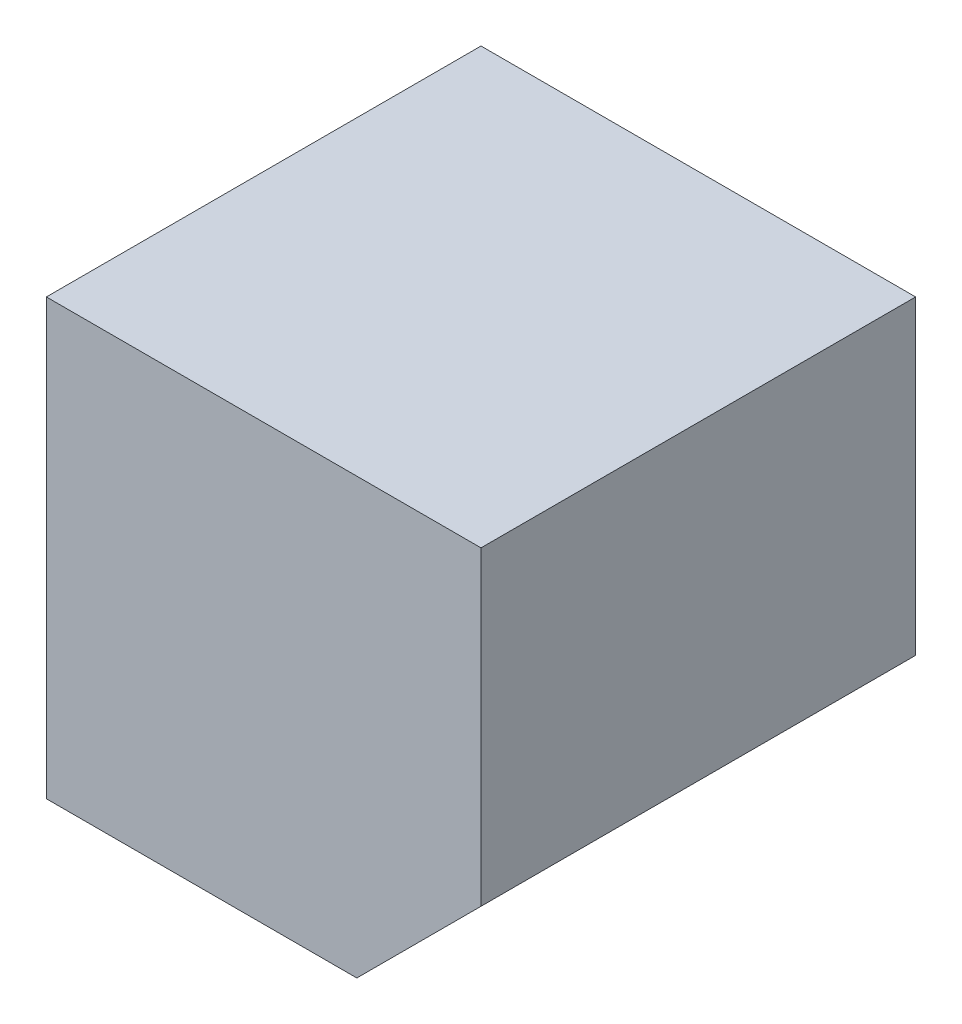
SolidWorks part; units mm, degrees
ref_plane "Front Plane" through (0, 0, 0) normal (0, 0, 1) x (1, 0, 0)
ref_plane "Top Plane" through (0, 0, 0) normal (0, 1, 0) x (1, 0, 0)
ref_plane "Right Plane" through (0, 0, 0) normal (1, 0, 0) x (0, 0, -1)
sketch "Sketch1" plane through (0, 0, 0) normal (0, 0, 1) x (1, 0, 0)
  line L0 (381, -889) -> (889, -381)
  line L1 (889, 889) -> (-889, 889)
  line L2 (889, 889) -> (889, -381)
  line L3 (381, -889) -> (-889, -889)
  line L4 (-889, 889) -> (-889, -889)
  line L5 (889, 889) -> (-889, -889) construction
  line L6 (635, -635) -> (-889, 889) construction
  point P0 (0, 0)
  point P8 (635, -635)
  dimension "D1" = 1778
  dimension "D2" = 1270
extrude "Boss-Extrude1" add sketch "Sketch1" along normal mid plane 1778
